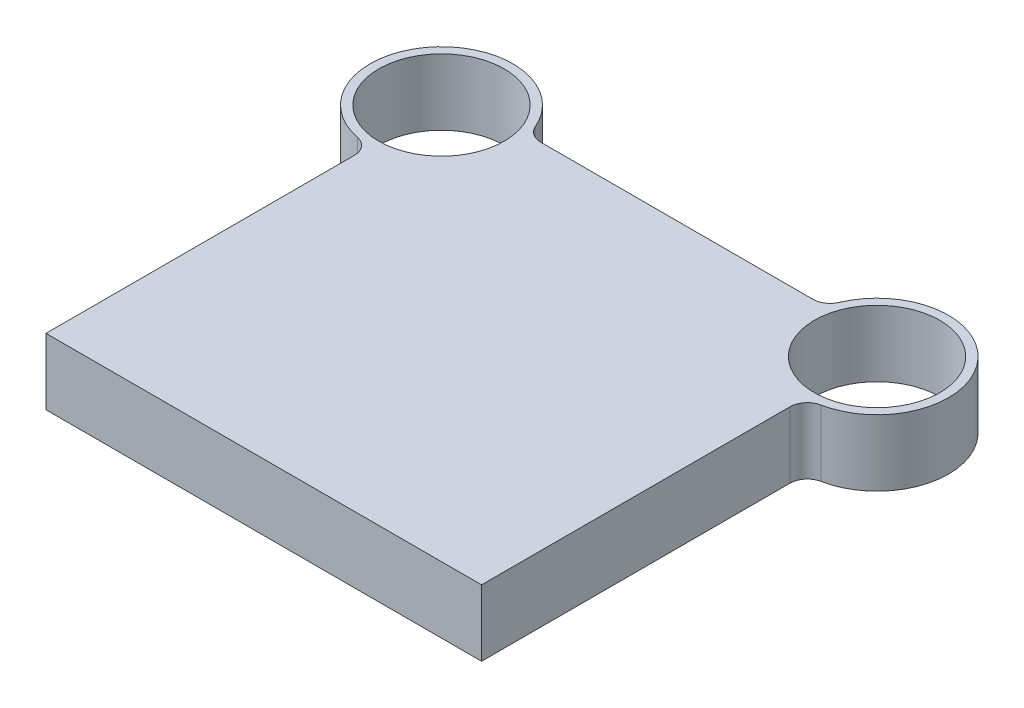
SolidWorks part; units mm, degrees
ref_plane "Front Plane" through (0, 0, 0) normal (0, 0, 1) x (1, 0, 0)
ref_plane "Top Plane" through (0, 0, 0) normal (0, 1, 0) x (1, 0, 0)
ref_plane "Right Plane" through (0, 0, 0) normal (1, 0, 0) x (0, 0, -1)
sketch "Sketch1" plane through (0, 0, 0) normal (0, 1, 0) x (1, 0, 0)
  line L0 (125, 0) -> (-125, 0)
  line L1 (-125, 0) -> (-125, 186)
  line L2 (0, 0) -> (0, 237) construction
  line L3 (85.2382, 237) -> (-85.2382, 237)
  line L4 (125, 0) -> (125, 186)
  arc A0 (-85.2382, 237) -> (-125, 186) centre (-125, 227) ccw
  circle A1 centre (-125, 227) radius 36
  circle A2 centre (125, 227) radius 36
  arc A3 (85.2382, 237) -> (125, 186) centre (125, 227) cw
  dimension "D3" = 82
  dimension "D4" = 72
  dimension "D1" = 227
  dimension "D2" = 237
  dimension "D5" = 250
  dimension "D6" = 250
extrude "Boss-Extrude1" add sketch "Sketch1" along normal blind 38
fillet "Fillet1" radius 10 4 edges at (-125, 19, -186) (125, 19, -186) (85.2382, 19, -237) (-85.2382, 19, -237)
